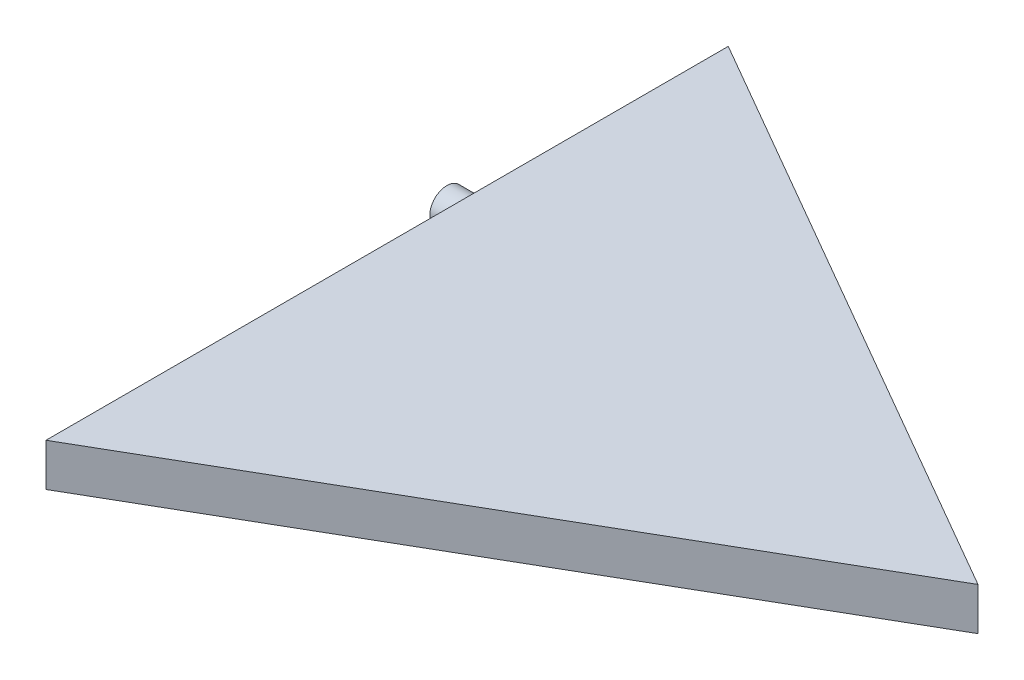
SolidWorks part; units mm, degrees
ref_plane "Front Plane" through (0, 0, 0) normal (0, 0, 1) x (1, 0, 0)
ref_plane "Top Plane" through (0, 0, 0) normal (0, 1, 0) x (1, 0, 0)
ref_plane "Right Plane" through (0, 0, 0) normal (1, 0, 0) x (0, 0, -1)
sketch "Sketch1" plane through (0, 0, 0) normal (0, 1, 0) x (1, 0, 0)
  line L0 (-69.282, 40) -> (0, 0)
  line L2 (-69.282, -40) -> (-69.282, 40)
  line L5 (-69.282, -40) -> (0, 0) construction
  line L6 (-69.282, 40) -> (0, 0) construction
  line L7 (-69.282, -40) -> (0, 0)
  point P1 (0, 0)
  dimension "D1" = 80
  dimension "D2" = 80
  dimension "D3" = 80
extrude "Boss-Extrude1" add sketch "Sketch1" along normal blind 5
sketch "Sketch2" plane through (-69.282, 0, 0) normal (-1, 0, 0) x (0, 0, 1)
  line L0 (40, 5) -> (40, 0) construction
  circle A0 centre (-10, 2.3602) radius 2
  dimension "D1" = 4
  dimension "D2" = 50
extrude "Boss-Extrude2" add sketch "Sketch2" along normal blind 3
